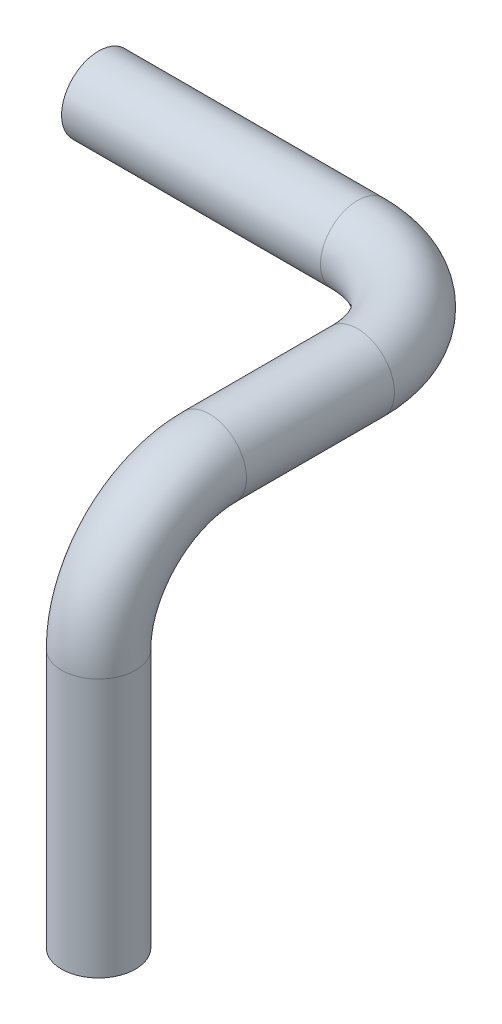
SolidWorks part; units mm, degrees
ref_plane "Front Plane" through (0, 0, 0) normal (0, 0, 1) x (1, 0, 0)
ref_plane "Top Plane" through (0, 0, 0) normal (0, 1, 0) x (1, 0, 0)
ref_plane "Right Plane" through (0, 0, 0) normal (1, 0, 0) x (0, 0, -1)
sketch3d "3DSketch1"
  line L0 (0, 254, 0) -> (177.8, 254, 0)
  line L1 (254, 254, 76.2) -> (254, 254, 177.8)
  line L2 (254, 177.8, 254) -> (254, 0, 254)
  arc A0 (254, 177.8, 254) -> (254, 254, 177.8) centre (254, 177.8, 177.8) ccw
  arc A1 (254, 254, 76.2) -> (177.8, 254, 0) centre (177.8, 254, 76.2) ccw
  point P0 (0, 254, 0)
  point P5 (0, 0, 0)
  point P6 (0, 0, 0)
  point P7 (0, 0, 0)
  point P8 (0, 0, 0)
  point P11 (254, 254, 254)
  point P12 (177.8, 177.8, 177.8)
  point P15 (254, 254, 0)
  point P16 (177.8, 330.2, 76.2)
  dimension "D1" = 76.2
sweep "Sweep1" add path "3DSketch1" circular profile diameter 50.8 parameters "D3"=50.8
shell "Shell2" thickness 2.54
